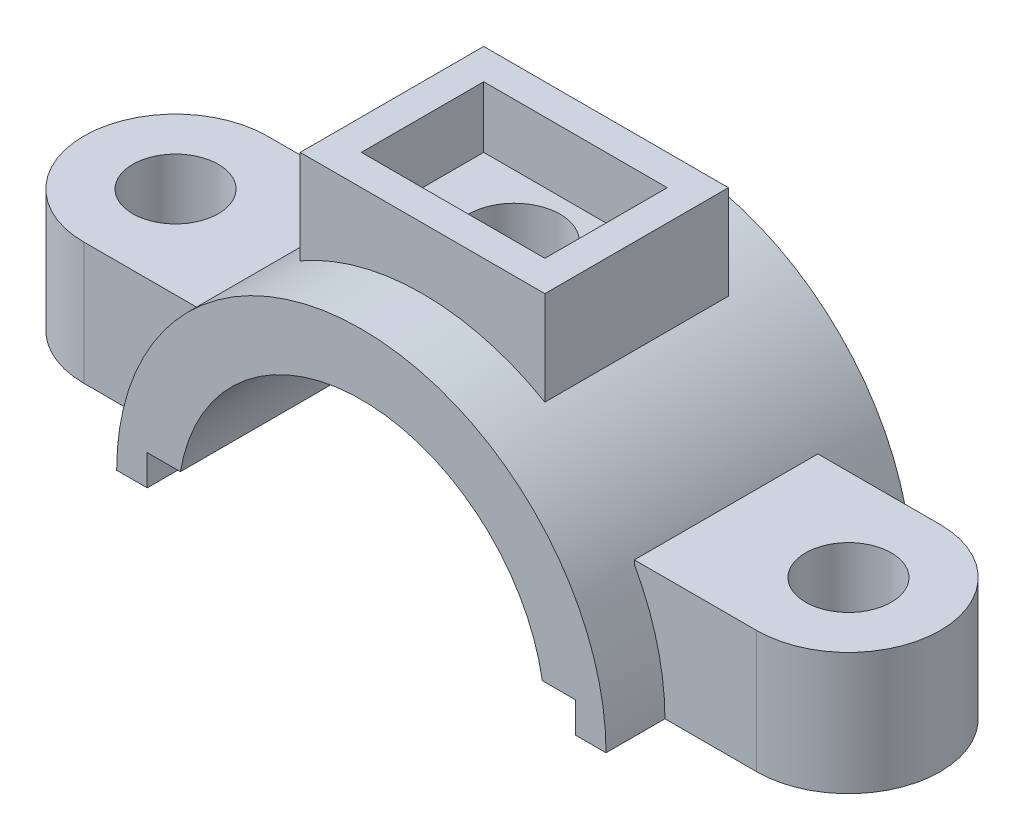
SolidWorks part; units mm, degrees
ref_plane "Front Plane" through (0, 0, 0) normal (0, 0, 1) x (1, 0, 0)
ref_plane "Top Plane" through (0, 0, 0) normal (0, 1, 0) x (1, 0, 0)
ref_plane "Right Plane" through (0, 0, 0) normal (1, 0, 0) x (0, 0, -1)
sketch "Sketch1" plane through (0, 0, 0) normal (0, 0, 1) x (1, 0, 0)
  line L0 (-145.3178, 0) -> (126.0462, 0) construction
  line L1 (-40, 0) -> (-35, 0)
  line L2 (-35, 0) -> (-35, 5)
  line L3 (-35, 5) -> (-29.5804, 5)
  line L4 (40, 0) -> (35, 0)
  line L5 (35, 0) -> (35, 5)
  line L6 (35, 5) -> (29.5804, 5)
  arc A0 (40, 0) -> (-40, 0) centre (0, 0) ccw
  arc A1 (29.5804, 5) -> (-29.5804, 5) centre (0, 0) ccw
  dimension "D1" = 80
  dimension "D2" = 60
  dimension "D3" = 5
  dimension "D4" = 5
  dimension "D5" = 5
  dimension "D6" = 5
extrude "Boss-Extrude1" add sketch "Sketch1" along normal mid plane 50
sketch "Sketch2" plane through (0, 0, 0) normal (0, 1, 0) x (1, 0, 0)
  line L0 (0, 32.6775) -> (0, -33.4294) construction
  line L1 (-55, 32.6775) -> (-55, -33.4294) construction
  line L2 (55, 32.6775) -> (55, -33.4294) construction
  line L4 (35, 14.624) -> (35, -15.376)
  line L5 (55, 14.624) -> (35, 14.624)
  line L6 (55, -15.376) -> (35, -15.376)
  line L7 (-55, -15.376) -> (-35, -15.376)
  line L8 (-55, 14.624) -> (-35, 14.624)
  line L9 (-35, -15.376) -> (-35, 14.624)
  arc A0 (55, -15.376) -> (55, 14.624) centre (55, -0.376) ccw
  arc A1 (-55, -15.376) -> (-55, 14.624) centre (-55, -0.376) cw
  dimension "D3" = 30
  dimension "D4" = 20
  dimension "D1" = 55
  dimension "D2" = 55
extrude "Boss-Extrude3" add sketch "Sketch2" along normal blind 20
sketch "Sketch3" plane through (0, 20, 0) normal (0, 1, 0) x (1, 0, 0)
  circle A0 centre (55, -0.376) radius 7
  dimension "D1" = 14
extrude "Cut-Extrude1" cut sketch "Sketch3" against normal blind 20
sketch "Sketch4" plane through (0, 20, 0) normal (0, 1, 0) x (1, 0, 0)
  circle A0 centre (-55, -0.376) radius 7
  dimension "D1" = 14
extrude "Cut-Extrude2" cut sketch "Sketch4" against normal blind 20
ref_plane "Plane1" through (0, 50, 0) normal (0, 1, 0) x (1, 0, 0)
sketch "Sketch5" plane through (0, 50, 0) normal (0, 1, 0) x (1, 0, 0)
  line L0 (0, 63.3508) -> (0, -68.5549) construction
  line L1 (-113.491, 0) -> (95.4765, 0) construction
  line L3 (-20, 15) -> (20, 15)
  line L4 (-20, 15) -> (-20, -15)
  line L5 (-20, -15) -> (20, -15)
  line L6 (20, 15) -> (20, -15)
  line L7 (-20, 15) -> (20, -15) construction
  line L8 (-20, -15) -> (20, 15) construction
  point P5 (0, 0)
  dimension "D1" = 40
  dimension "D2" = 30
extrude "Boss-Extrude4" add sketch "Sketch5" against normal up to surface (15.359 mm away)
sketch "Sketch6" plane through (0, 50, 0) normal (0, 1, 0) x (1, 0, 0)
  line L0 (20, 15) -> (-20, 15) construction
  line L1 (-15, 10) -> (15, 10)
  line L2 (-15, 10) -> (-15, -10)
  line L3 (-15, -10) -> (15, -10)
  line L4 (15, 10) -> (15, -10)
  line L5 (-20, 15) -> (-20, -15) construction
  line L6 (20, -15) -> (20, 15) construction
  line L7 (-20, -15) -> (20, -15) construction
  dimension "D1" = 5
  dimension "D2" = 5
  dimension "D3" = 5
  dimension "D4" = 5
extrude "Cut-Extrude3" cut sketch "Sketch6" against normal blind 10
sketch "Sketch7" plane through (0, 40, 0) normal (0, 1, 0) x (1, 0, 0)
  circle A0 centre (0, 0) radius 7.5
  dimension "D1" = 15
extrude "Cut-Extrude4" cut sketch "Sketch7" against normal up to next
